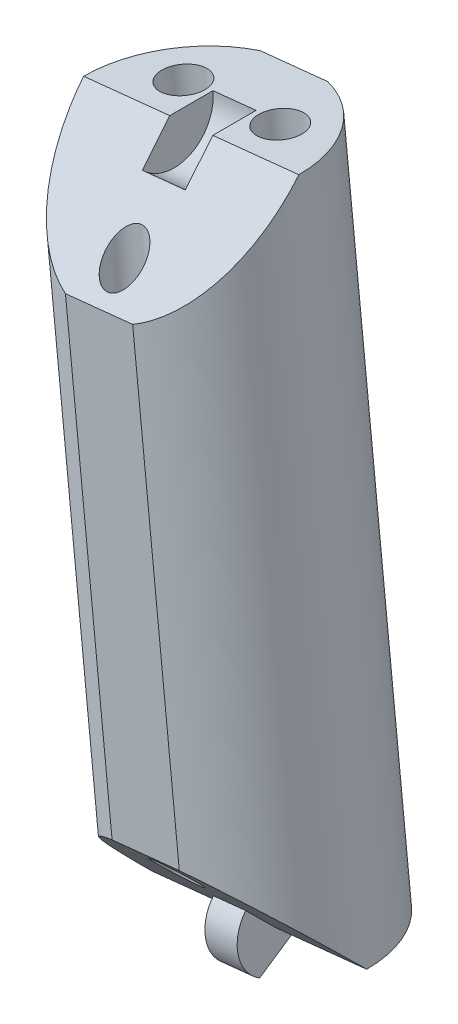
SolidWorks part; units mm, degrees
ref_plane "Front Plane" through (0, 0, 0) normal (0, 0, 1) x (1, 0, 0)
ref_plane "Top Plane" through (0, 0, 0) normal (0, 1, 0) x (1, 0, 0)
ref_plane "Right Plane" through (0, 0, 0) normal (1, 0, 0) x (0, 0, -1)
sketch "Sketch2" plane through (0, 0, 0) normal (0, 0, 1) x (1, 0, 0)
  line L0 (0, 0) -> (90, 0)
  line L1 (90, 0) -> (90, 120)
  line L2 (90, 120) -> (0, 120)
  line L3 (0, 120) -> (0, 0)
  line L4 (0, 120) -> (-10, 120)
  line L5 (-10, 120) -> (-10, 16.9491)
  line L6 (-10, 120) -> (57.5, 127)
  line L7 (57.5, 127) -> (90, 124)
  line L8 (90, 120) -> (99, 60)
  line L10 (90, 124) -> (90, 120)
  line L11 (5.9147, 0) -> (5.9147, -25)
  line L12 (5.9147, -25) -> (-4.0853, -25)
  line L13 (-4.0853, -29) -> (-4.0853, 0)
  line L14 (80, 0) -> (80, -25)
  line L15 (80, -25) -> (90, -25)
  line L16 (90, -29) -> (90, 0)
  line L17 (15.7927, 122.6748) -> (5.4776, 222.1414)
  line L18 (5.4776, 222.1414) -> (21.3923, 223.7918)
  line L19 (21.3923, 223.7918) -> (31.7073, 124.3252)
  line L20 (7.6492, 201.201) -> (23.5639, 202.8514)
  line L21 (10.9066, 169.7905) -> (26.8212, 171.441)
  line L22 (-10, 120) -> (-20.0396, 216.8108)
  line L23 (-20.0396, 216.8108) -> (-4.125, 218.4612)
  line L24 (-4.125, 218.4612) -> (5.9147, 121.6504)
  line L25 (-17.926, 196.4296) -> (-2.0114, 198.08)
  line L26 (-14.7556, 165.8578) -> (1.159, 167.5082)
  line L27 (57.5, 127) -> (46.9095, 229.1223)
  line L28 (46.9095, 229.1223) -> (30.9949, 227.4719)
  line L29 (30.9949, 227.4719) -> (41.5853, 125.3496)
  line L30 (33.2245, 205.9725) -> (49.1391, 207.6229)
  line L31 (36.5688, 173.7233) -> (52.4835, 175.3737)
  line L34 (90, 124) -> (99.1917, 223.5767)
  line L35 (99.1917, 223.5767) -> (83.2594, 225.0473)
  line L36 (83.2594, 225.0473) -> (74.0677, 125.4707)
  line L38 (81.3243, 204.0838) -> (97.2566, 202.6132)
  line L39 (78.4217, 172.6386) -> (94.354, 171.1679)
  line L40 (62.4078, 79.6749) -> (57.5, 127) construction
  line L41 (41.5853, 125.3496) -> (46.4931, 78.0244) construction
  line L42 (46.4931, 78.0244) -> (62.4078, 79.6749) construction
  line L43 (31.7073, 124.3252) -> (36.6151, 77.0001) construction
  line L44 (36.6151, 77.0001) -> (20.7005, 75.3496) construction
  line L45 (20.7005, 75.3496) -> (15.7927, 122.6748) construction
  line L46 (5.9147, 121.6504) -> (10.8224, 74.3253) construction
  line L47 (10.8224, 74.3253) -> (-5.0922, 72.6749) construction
  line L48 (-5.0922, 72.6749) -> (-10, 120) construction
  line L49 (74.0677, 125.4707) -> (69.6944, 78.0931) construction
  line L50 (69.6944, 78.0931) -> (85.7624, 78.0931) construction
  line L51 (85.7624, 78.0931) -> (90, 124) construction
  line L52 (-12.0823, 217.636) -> (10.4873, 0) construction
  line L53 (13.4349, 222.9666) -> (36.5574, 0) construction
  line L54 (38.9522, 228.2971) -> (62.6275, 0) construction
  line L55 (91.2256, 224.312) -> (70.5198, 0) construction
  line L59 (99, 60) -> (93.5277, 44.9649)
  line L60 (99, 60) -> (169.4769, 34.3485)
  line L61 (169.4769, 34.3485) -> (164.0046, 19.3134)
  line L62 (164.0046, 19.3134) -> (93.5277, 44.9649)
  line L63 (90, -2) -> (100, -2)
  line L64 (141.2862, 44.6091) -> (135.8138, 29.574)
  line L65 (99, 60) -> (55.7741, 75.7329) construction
  line L66 (55.7741, 75.7329) -> (50.3018, 60.6978) construction
  line L67 (100, -2) -> (100, -29)
  line L70 (-4.0853, -2) -> (-14.0853, -2)
  line L71 (-14.0853, -2) -> (-14.0853, -29)
  line L74 (-4.0853, 0) -> (0, 0)
  line L75 (-14.0853, -29) -> (-14.0853, -112.587)
  line L76 (-14.0853, -112.587) -> (100, -112.587)
  line L77 (100, -112.587) -> (100, -29)
  line L78 (-14.0853, -29) -> (100, -29)
  line L79 (-14.0853, -14.5) -> (100, -14.5) construction
  line L80 (31.7073, -112.587) -> (31.7073, -122.6232)
  line L81 (31.7073, -122.6232) -> (42.9573, -122.6232)
  line L82 (42.9573, -122.6232) -> (42.9573, -112.587)
  line L83 (-14.0853, -112.587) -> (-88.3667, -112.587)
  line L84 (-88.3667, -112.587) -> (-88.3667, -128.2699)
  line L85 (-88.3667, -128.2699) -> (169.4958, -128.2699)
  line L86 (169.4958, -128.2699) -> (169.4958, -112.587)
  line L87 (169.4958, -112.587) -> (100, -112.587)
  line L88 (90, 60) -> (-10, 60) construction
  line L89 (50.3018, 60.6978) -> (93.5277, 44.9649) construction
  line L90 (87.2806, 55.7521) -> (166.7408, 26.8309) construction
  line L91 (87.2806, 55.7521) -> (82.1749, 52.5336) construction
  line L92 (82.1749, 52.5336) -> (77.3257, 0) construction
  line L93 (83.1185, 56.6957) -> (86.337, 51.59) construction
  arc A0 (-10, 16.9491) -> (-4.0853, 0) centre (14.9876, 16.1624) ccw
  arc A1 (93.5277, 44.9649) -> (90, 0) centre (-126.4069, 39.5988) cw
  point P42 (41.1818, 206.7977)
  point P100 (84.7278, 54.1428)
  point P101 (84.7278, 54.1428)
  dimension "D11" = 47.3684
  dimension "D35" = 9
  dimension "D32" = 220
  dimension "D36" = 25
  dimension "D1" = 120
  dimension "D2" = 90
  dimension "D3" = 10
  dimension "D5" = 67.862
  dimension "D6" = 7
  dimension "D7" = 4
  dimension "D8" = 16
  dimension "D9" = 16
  dimension "D10" = 100
  dimension "D12" = 31.5789
  dimension "D13" = 16
  dimension "D14" = 16
  dimension "D15" = 16
  dimension "D16" = 25.7927
  dimension "D17" = 100
  dimension "D18" = 21.0526
  dimension "D19" = 31.5789
  dimension "D20" = 97.33
  dimension "D21" = 102.67
  dimension "D22" = 20.4905
  dimension "D23" = 30.7358
  dimension "D24" = 21.6147
  dimension "D25" = 32.4221
  dimension "D26" = 25
  dimension "D28" = 25
  dimension "D29" = 75
  dimension "D30" = 47.5789
  dimension "D31" = 30
  dimension "D33" = 46
  dimension "D34" = 20
  dimension "D37" = 2
  dimension "D38" = 2
  dimension "D39" = 27
  dimension "D40" = 10
  dimension "D41" = 10
  dimension "D42" = 27
  dimension "D43" = 14.5
  dimension "D44" = 127.5
ref_plane "Plane1" through (87.2806, 55.7521, 0) normal (-0.846, -0.5333, 0) x (0, 0, 1)
ref_plane "Plane2" through (82.1749, 52.5336, 0) normal (-0.0919, -0.9958, 0) x (-0.9958, 0.0919, 0)
ref_plane "Plane3" through (91.2256, 224.312, 0) normal (-0.0919, -0.9958, 0) x (-0.9958, 0.0919, 0)
ref_plane "Plane4" through (38.9522, 228.2971, 0) normal (0.1032, -0.9947, 0) x (-0.9947, -0.1032, 0)
ref_plane "Plane5" through (13.4349, 222.9666, 0) normal (0.1032, -0.9947, 0) x (-0.9947, -0.1032, 0)
ref_plane "Plane7" through (166.7408, 26.8309, 0) normal (0.9397, -0.342, 0) x (0, 0, -1)
ref_plane "Plane8" through (110.4217, -40.1902, 0) normal (0.9397, -0.342, 0) x (0, 0, -1)
ref_plane "Plane9" through (19.3664, 209.803, 0) normal (-0.0919, -0.9958, 0) x (-0.9958, 0.0919, 0)
ref_plane "Plane10" through (16.4638, 178.3578, 0) normal (-0.0919, -0.9958, 0) x (-0.9958, 0.0919, 0)
ref_plane "Plane11" through (-20.7793, 200.3721, 0) normal (0.1032, -0.9947, 0) x (-0.9947, -0.1032, 0)
ref_plane "Plane12" through (-17.435, 168.1229, 0) normal (0.1032, -0.9947, 0) x (-0.9947, -0.1032, 0)
ref_plane "Plane13" through (-20.5619, 198.2754, 0) normal (0.1032, -0.9947, 0) x (-0.9947, -0.1032, 0)
ref_plane "Plane14" through (-17.3045, 166.8649, 0) normal (0.1032, -0.9947, 0) x (-0.9947, -0.1032, 0)
ref_plane "Plane15" through (-12.0823, 217.636, 0) normal (0.1032, -0.9947, 0) x (-0.9947, -0.1032, 0)
ref_plane "Plane16" through (-20.3445, 196.1788, 0) normal (0.1032, -0.9947, 0) x (-0.9947, -0.1032, 0)
ref_plane "Plane17" through (-17.1741, 165.607, 0) normal (0.1032, -0.9947, 0) x (-0.9947, -0.1032, 0)
ref_plane "Plane18" through (12.1098, 131.1899, 0) normal (-0.0919, -0.9958, 0) x (-0.9958, 0.0919, 0)
ref_plane "Plane19" through (-12.4184, 119.7492, 0) normal (0.1032, -0.9947, 0) x (-0.9947, -0.1032, 0)
ref_plane "Plane20" through (0, 0, 0) normal (0, 0, 1) x (0.1032, -0.9947, 0)
ref_plane "Plane21" through (0, 0, 0) normal (0, 0, 1) x (-0.0919, -0.9958, 0)
ref_plane "Plane22" through (10.3758, 1.076, 0) normal (-0.9947, -0.1032, 0) x (0.1032, -0.9947, 0)
ref_plane "Plane23" through (36.1684, 3.7508, 0) normal (-0.9947, -0.1032, 0) x (0.1032, -0.9947, 0)
ref_plane "Plane24" through (61.9611, 6.4256, 0) normal (-0.9947, -0.1032, 0) x (0.1032, -0.9947, 0)
ref_plane "Plane25" through (69.924, -6.4545, 0) normal (-0.9958, 0.0919, 0) x (-0.0919, -0.9958, 0)
sketch "Sketch3" plane through (-20.3445, 196.1788, 0) normal (0.1032, -0.9947, 0) x (-0.9947, -0.1032, 0)
  line L0 (-2.4314, 0) -> (-18.4314, 0) construction
  circle A0 centre (-10.4314, 0) radius 8
  dimension "D1" = 16
extrude "Boss-Extrude1" add sketch "Sketch3" along normal blind 48.6332
sketch "Sketch4" plane through (10.3758, 1.076, 0) normal (-0.9947, -0.1032, 0) x (0.1032, -0.9947, 0)
  line L0 (-197.2309, 0) -> (-189.2309, 8)
  line L1 (-197.2309, 8) -> (-197.2309, -8) construction
  line L2 (-148.5977, 8) -> (-197.2309, 8) construction
  line L3 (-189.2309, 8) -> (-197.2309, 8)
  line L4 (-197.2309, 8) -> (-197.2309, 0)
  line L5 (-156.5977, 8) -> (-148.5977, 8)
  line L6 (-148.5977, 8) -> (-148.5977, 0)
  line L7 (-217.7214, 0) -> (1.0818, 0) construction
  line L8 (-148.5977, 0) -> (-156.5977, 8)
  dimension "D1" = 45
  dimension "D2" = 45
extrude "Cut-Extrude1" cut sketch "Sketch4" against normal through all and the other way through all
sketch "Sketch5" plane through (10.3758, 1.076, 0) normal (-0.9947, -0.1032, 0) x (0.1032, -0.9947, 0)
  line L1 (-148.5977, -2.8) -> (-146.1728, 1.4)
  line L6 (-148.5977, 0) -> (-156.5977, 8) construction
  line L11 (-148.5977, -8) -> (-148.5977, 0) construction
  line L12 (-150.5776, 1.9799) -> (-148.5977, 0)
  line L13 (-148.5977, 0) -> (-148.5977, -2.8)
  arc A3 (-150.5776, 1.9799) -> (-146.1728, 1.4) centre (-148.5977, 0) cw
  dimension "D2" = 2.8
  dimension "D1" = 30
  dimension "D3" = 2.8
extrude "Boss-Extrude2" add sketch "Sketch5" along normal mid plane 2.4
sketch "Sketch7" plane through (10.3758, 1.076, 0) normal (-0.9947, -0.1032, 0) x (0.1032, -0.9947, 0)
  line L6 (-197.2309, 0) -> (-197.2309, -8) construction
  line L7 (-189.2309, 8) -> (-197.2309, 0) construction
  line L8 (-194.9681, 2.2627) -> (-197.2309, 0)
  line L9 (-197.2309, 0) -> (-197.2309, -3.2)
  arc A1 (-197.2309, -3.2) -> (-194.9681, 2.2627) centre (-197.2309, 0) ccw
  dimension "D1" = 3.2
extrude "Cut-Extrude2" cut sketch "Sketch7" against normal mid plane 3.2
sketch "Sketch8" plane through (-20.3445, 196.1788, 0) normal (-0.1032, 0.9947, 0) x (0.9947, 0.1032, 0)
  line L0 (2.4314, 0) -> (18.4314, 0) construction
  circle A0 centre (10.4314, -5.5) radius 1.4
  circle A1 centre (6.8314, 3) radius 1.6
  circle A2 centre (14.0314, 3) radius 1.6
  point P9 (10.4314, 0)
  dimension "D1" = 3.2
  dimension "D2" = 3.2
  dimension "D3" = 2.8
  dimension "D4" = 3
  dimension "D5" = 5.5
  dimension "D6" = 3.6
  dimension "D7" = 3.6
  dimension "D8" = 3
extrude "Cut-Extrude3" cut sketch "Sketch8" against normal through all and the other way through all
sketch "Sketch9" plane through (-20.3445, 196.1788, 0) normal (-0.1032, 0.9947, 0) x (0.9947, 0.1032, 0)
  line L0 (7.9334, 7.6) -> (12.9294, 7.6)
  line L1 (-101.1265, 0) -> (155.3606, 0) construction
  line L2 (7.9334, -7.6) -> (12.9294, -7.6)
  arc A0 (18.4314, 0) -> (2.4314, 0) centre (10.4314, 0) ccw construction
  arc A1 (7.9334, 7.6) -> (12.9294, 7.6) centre (10.4314, 0) cw
  arc A2 (2.4314, 0) -> (18.4314, 0) centre (10.4314, 0) ccw construction
  arc A3 (7.9334, -7.6) -> (12.9294, -7.6) centre (10.4314, 0) ccw
  dimension "D1" = 7.6
  dimension "D2" = 7.6
extrude "Cut-Extrude4" cut sketch "Sketch9" against normal through all
